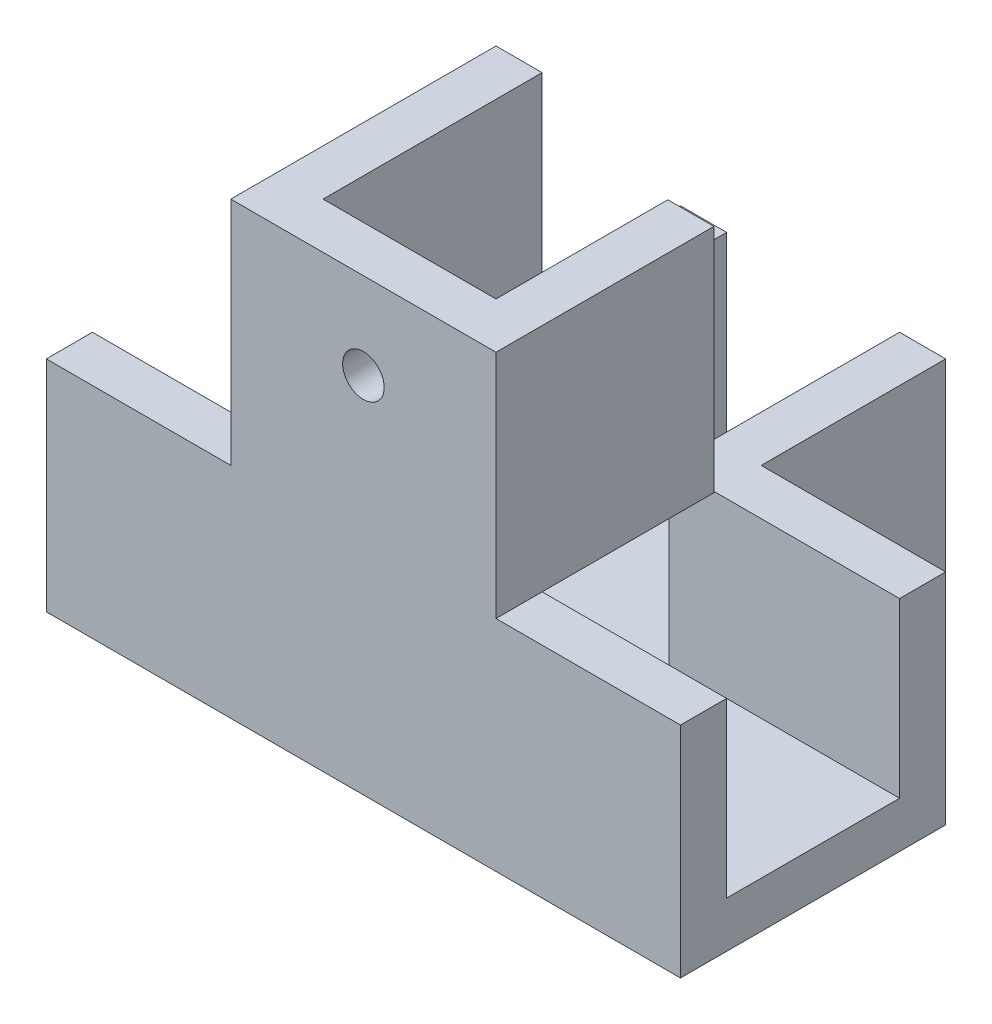
SolidWorks part; units mm, degrees
ref_plane "前视基准面" through (0, 0, 0) normal (0, 0, 1) x (1, 0, 0)
ref_plane "上视基准面" through (0, 0, 0) normal (0, 1, 0) x (1, 0, 0)
ref_plane "右视基准面" through (0, 0, 0) normal (1, 0, 0) x (0, 0, -1)
sketch "草图1" plane through (0, 0, 0) normal (0, 1, 0) x (1, 0, 0)
  line L0 (14.2449, 15.7755) -> (30.2449, 15.7755)
  line L1 (-24.7551, -3.2245) -> (30.2449, -3.2245)
  line L2 (-24.7551, -3.2245) -> (-24.7551, -7.2245)
  line L3 (-24.7551, -7.2245) -> (30.2449, -7.2245)
  line L4 (30.2449, -3.2245) -> (30.2449, -7.2245)
  line L5 (-24.7551, 15.7755) -> (-8.7551, 15.7755)
  line L6 (-24.7551, 15.7755) -> (-24.7551, 11.7755)
  line L7 (-24.7551, 11.7755) -> (-4.7551, 11.7755)
  line L8 (30.2449, 15.7755) -> (30.2449, 11.7755)
  line L9 (-7.5102, 11.7755) -> (-4.7551, 11.7755)
  line L10 (-8.7551, 15.7755) -> (-8.7551, 31.7755)
  line L11 (-8.7551, 31.7755) -> (-4.7551, 31.7755)
  line L12 (-4.7551, 11.7755) -> (-4.7551, 31.7755)
  line L13 (10.2449, 11.7755) -> (12.2449, 11.7755)
  line L14 (10.2449, 11.7755) -> (10.2449, 31.7755)
  line L15 (10.2449, 31.7755) -> (14.2449, 31.7755)
  line L16 (14.2449, 15.7755) -> (14.2449, 31.7755)
  line L17 (10.2449, 11.7755) -> (30.2449, 11.7755)
  dimension "D1" = 4
  dimension "D2" = 4
  dimension "D3" = 4
  dimension "D4" = 4
  dimension "D5" = 4
  dimension "D6" = 15
  dimension "D7" = 15
  dimension "D8" = 20
  dimension "D9" = 20
  dimension "D10" = 0
  dimension "D11" = 0
  dimension "D12" = 20
  dimension "D13" = 20
extrude "凸台-拉伸1" add sketch "草图1" along normal blind 15 contours L7 L12 L11 L10 L5 L6 | L13 L17 L8 L0 L16 L15 L14 | L4 L1 L2 L3
sketch "草图2" plane through (0, 0, 0) normal (0, -1, 0) x (1, 0, 0)
  line L0 (-8.7551, -15.7755) -> (-24.7551, -15.7755)
  line L1 (30.2449, -15.7755) -> (14.2449, -15.7755)
  line L2 (30.2449, -15.7755) -> (30.2449, 7.2245)
  line L3 (30.2449, 7.2245) -> (-24.7551, 7.2245)
  line L4 (-24.7551, -15.7755) -> (-24.7551, 7.2245)
  line L5 (14.2449, -31.7755) -> (-8.7551, -31.7755)
  line L6 (14.2449, -31.7755) -> (14.2449, -15.7755)
  line L8 (-8.7551, -31.7755) -> (-8.7551, -15.7755)
extrude "凸台-拉伸2" add sketch "草图2" along normal blind 4
sketch "草图3" plane through (0, 15, 0) normal (0, 1, 0) x (1, 0, 0)
  line L0 (-24.7551, -7.2245) -> (30.2449, -7.2245) construction
  line L1 (-8.7551, 15.7755) -> (-4.7551, 15.7755)
  line L2 (-8.7551, 15.7755) -> (-8.7551, -7.2245)
  line L3 (-8.7551, -7.2245) -> (-4.7551, -7.2245)
  line L4 (-4.7551, 15.7755) -> (-4.7551, -3.2245)
  line L5 (10.2449, 11.7755) -> (30.2449, 11.7755) construction
  line L6 (14.2449, 11.6755) -> (10.2449, 11.6755)
  line L7 (14.2449, 11.6755) -> (14.2449, -7.2245)
  line L8 (14.2449, -7.2245) -> (10.2449, -7.2245)
  line L9 (10.2449, 11.6755) -> (10.2449, -3.2245)
  line L10 (10.2449, -7.2245) -> (-4.7551, -7.2245)
  line L12 (10.2449, -3.2245) -> (-4.7551, -3.2245)
  dimension "D1" = 4
  dimension "D2" = 4
  dimension "D3" = 4
  dimension "D4" = 0.1
extrude "凸台-拉伸3" add sketch "草图3" along normal blind 20
sketch "草图4" plane through (0, -4, 0) normal (0, -1, 0) x (1, 0, 0)
  line L0 (-8.7551, -31.7755) -> (14.2449, -31.7755) construction
  circle A0 centre (2.7449, -24.2755) radius 1.8
  circle A1 centre (2.7449, -4.2755) radius 1.8
  dimension "D2" = 3.6
  dimension "D3" = 3.6
  dimension "D1" = 7.5
extrude "切除-拉伸1" cut sketch "草图4" against normal blind 20
sketch "草图5" plane through (0, 0, 7.2245) normal (0, 0, 1) x (1, 0, 0)
  line L0 (-8.7551, 35) -> (14.2449, 35) construction
  circle A0 centre (2.7449, 27.5) radius 1.8
  dimension "D1" = 7.5
  dimension "D2" = 3.6
extrude "切除-拉伸2" cut sketch "草图5" against normal blind 20
